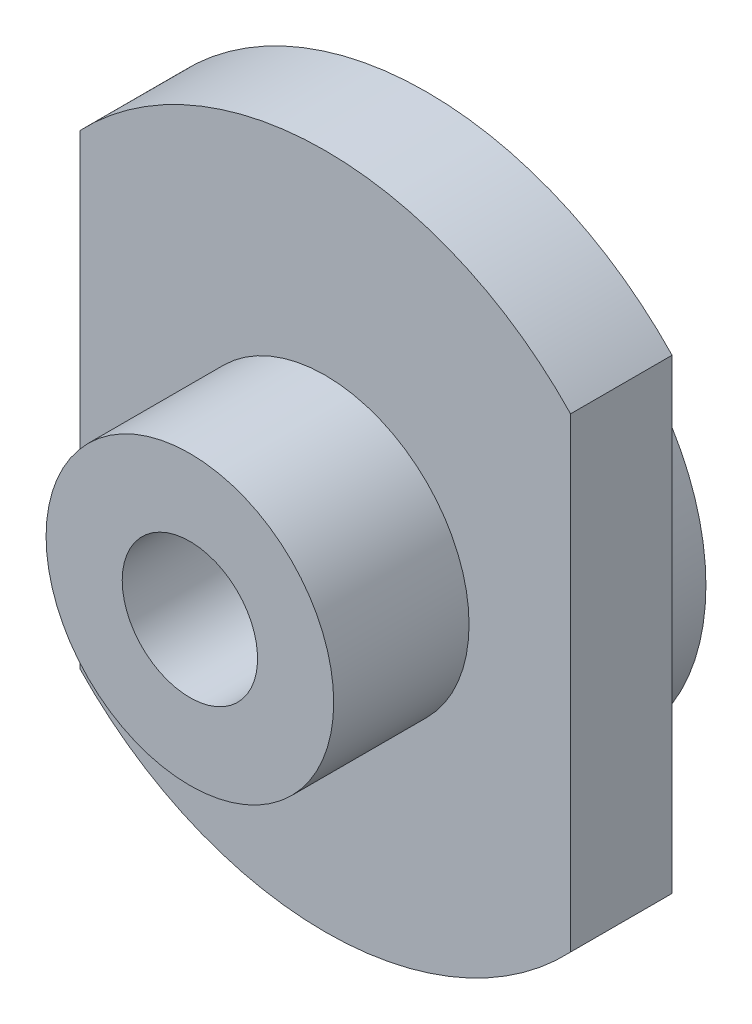
SolidWorks part; units mm, degrees
ref_plane "前基準面" through (0, 0, 0) normal (0, 0, 1) x (1, 0, 0)
ref_plane "上基準面" through (0, 0, 0) normal (0, 1, 0) x (1, 0, 0)
ref_plane "右基準面" through (0, 0, 0) normal (1, 0, 0) x (0, 0, -1)
sketch "草圖1" plane through (0, 0, 0) normal (0, 0, 1) x (1, 0, 0)
  circle A1 centre (0, 0) radius 17
  dimension "D1" = 34
extrude "填料-伸長1" add sketch "草圖1" along normal blind 34
sketch "草圖2" plane through (0, 0, 0) normal (0, 0, 1) x (1, 0, 0)
  circle A0 centre (0, 0) radius 40
  dimension "D1" = 80
extrude "填料-伸長2" add sketch "草圖2" along normal offset from surface (12 mm away) 18 from offset 6 up to face at (17, 0, 0)
sketch "草圖3" plane through (0, 0, 6) normal (0, 0, -1) x (-1, 0, 0)
  circle A0 centre (0, 0) radius 27
  dimension "D1" = 54
extrude "填料-伸長3" add sketch "草圖3" along normal up to surface (6 mm away) up to face at (17, 0, 0)
sketch "草圖4" plane through (0, 0, 0) normal (0, 0, -1) x (-1, 0, 0)
  circle A0 centre (0, 0) radius 12
  circle A1 centre (0, 0) radius 24
  dimension "D1" = 24
  dimension "D2" = 48
extrude "除料-伸長1" cut sketch "草圖4" against normal blind 9
sketch "草圖5" plane through (0, 0, 0) normal (0, 0, -1) x (-1, 0, 0)
  line L1 (-29, -40) -> (29, -40)
  line L2 (-29, -40) -> (-29, 40)
  line L3 (-29, 40) -> (29, 40)
  line L4 (29, -40) -> (29, 40)
  line L5 (-29, -40) -> (29, 40) construction
  line L6 (-29, 40) -> (29, -40) construction
  circle A0 centre (0, 0) radius 8
  circle A2 centre (0, 0) radius 40 construction
  dimension "D1" = 16
  dimension "58" = 58
extrude "除料-伸長2" cut sketch "草圖5" against normal through all flip side to cut
